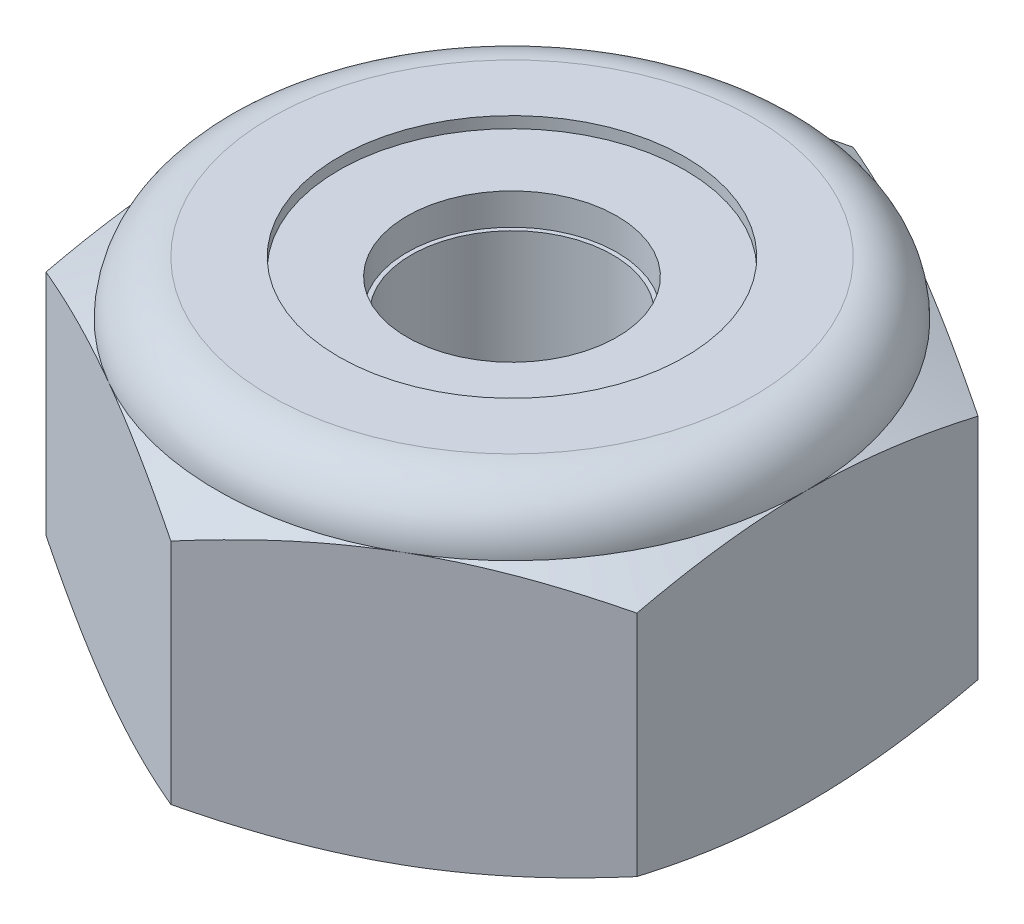
SolidWorks part; units mm, degrees
material "Alloy Steel"
ref_plane "Front" through (0, 0, 0) normal (0, 0, 1) x (1, 0, 0)
ref_plane "Top" through (0, 0, 0) normal (0, 1, 0) x (1, 0, 0)
ref_plane "Right" through (0, 0, 0) normal (1, 0, 0) x (0, 0, -1)
sketch "Sketch1" plane through (0, 0, 0) normal (0, 1, 0) x (1, 0, 0)
  line L1 (0, 4.5827) -> (-3.9688, 2.2914)
  line L2 (-3.9688, 2.2914) -> (-3.9688, -2.2914)
  line L3 (-3.9688, -2.2914) -> (0, -4.5827)
  line L4 (0, -4.5827) -> (3.9688, -2.2914)
  line L5 (3.9688, -2.2914) -> (3.9687, 2.2914)
  line L6 (3.9687, 2.2914) -> (0, 4.5827)
  circle A0 centre (0, 0) radius 3.9688 construction
  dimension "Hex Flats" = 7.9375
extrude "Extrude1" add sketch "Sketch1" along normal blind 4.3656
sketch "Sketch2" plane through (0, 0, 0) normal (1, 0, 0) x (0, 0, -1)
  line L0 (-1.7526, 0) -> (-1.7526, 4.3656) construction
  line L1 (0, 0) -> (1.7526, 0)
  line L2 (0, 0) -> (0, 4.3656)
  line L3 (0, 4.3656) -> (1.7526, 4.3656)
  line L4 (1.7526, 0) -> (1.7526, 4.3656)
  line L5 (-2.2914, 4.3656) -> (2.2914, 4.3656) construction
  line L7 (0, -1.7526) -> (0, 0) construction
  dimension "Thread Dia" = 3.5052
revolve "Revolve1" add sketch "Sketch2" angle 360 about L7
sketch "Sketch3" plane through (0, 0, 0) normal (1, 0, 0) x (0, 0, -1)
  line L0 (1.7526, 4.3656) -> (-1.7526, 4.3656) construction
  line L1 (-1.7526, 4.3656) -> (-1.7526, 3.5719) construction
  line L2 (-1.7526, 3.5719) -> (1.7526, 4.3656) construction
  line L3 (1.7526, 4.3656) -> (1.7745, 4.2689) construction
  line L4 (1.7745, 4.2689) -> (1.9279, 3.5915)
  line L5 (1.9279, 3.5915) -> (1.4541, 3.7385)
  line L6 (1.4541, 3.7385) -> (1.4103, 3.932)
  line L7 (1.4103, 3.932) -> (1.7745, 4.2689)
  line L8 (1.4322, 3.8353) -> (1.8512, 3.9302) construction
  line L9 (1.7526, 4.3656) -> (1.7526, 3.9078) construction
  line L10 (1.7526, 3.9078) -> (-1.7526, 3.1141) construction
  line L11 (-1.7526, 3.1141) -> (-1.7526, 3.5719) construction
  line L12 (-0.1935, 4.3656) -> (0.1935, 2.6563) construction
  line L13 (-1.7526, 0) -> (-1.7526, 4.3656) construction
  line L14 (0, 4.3656) -> (1.7526, 4.3656) construction
  line L15 (1.7526, 0) -> (1.7526, 4.3656) construction
  point P13 (0, 3.511)
  dimension "D1" = 0.0992
  dimension "D2" = 0.1984
  dimension "Thread Pitch" = 0.7937
  dimension "D4" = 60
  dimension "D5" = 0.7937
revolve "Cut-Revolve1" cut sketch "Sketch3" angle 360 about L12
pattern_linear "LPattern1" count 6 spacing 0.7937 along (0, -1, 0) count 2 spacing 0.7937 along (0, 1, 0) of "Cut-Revolve1"
sketch "Sketch4" plane through (0, 0, 0) normal (1, 0, 0) x (0, 0, -1)
  line L0 (0, 4.3656) -> (1.7526, 4.3656)
  line L1 (1.7526, 4.3656) -> (1.4103, 4.206)
  line L2 (1.4103, 4.206) -> (1.4103, 0.1596)
  line L3 (1.4103, 0.1596) -> (1.7526, 0)
  line L4 (1.7526, 0) -> (0, 0)
  line L5 (0, 0) -> (0, 4.3656)
  line L6 (1.7526, 0) -> (1.7526, 4.3656) construction
  line L7 (0, 4.3656) -> (1.7526, 4.3656) construction
  line L8 (0, 0) -> (1.7526, 0) construction
  line L9 (0, 0) -> (0, 4.3656) construction
  line L10 (0, 4.3656) -> (0, 4.7433) construction
  dimension "D1" = 25
revolve "Cut-Revolve2" cut sketch "Sketch4" angle 360 about L10
combine bodies "Combine1" operation type subtract main body 112 bodies to subtract 111
sketch "Sketch5" plane through (0, 0, 0) normal (1, 0, 0) x (0, 0, -1)
  line L0 (0, 0) -> (3.9688, 0)
  line L1 (3.9688, 0) -> (4.5827, 0.2863)
  line L2 (4.5827, 0.2863) -> (4.5827, 3.3517)
  line L3 (4.5827, 3.3517) -> (3.9687, 3.638)
  line L4 (3.2411, 4.3656) -> (3.2411, 5.6356)
  line L5 (3.2411, 5.6356) -> (5.8527, 5.6356)
  line L6 (5.8527, 5.6356) -> (5.8527, -1.27)
  line L7 (5.8527, -1.27) -> (0, -1.27)
  line L8 (0, -1.27) -> (0, 0)
  line L9 (3.9687, 3.638) -> (3.9688, 0) construction
  line L10 (0, 0) -> (1.7526, 0) construction
  line L13 (4.5827, 1.819) -> (5.8527, 1.819) construction
  line L14 (4.5827, 4.3656) -> (4.5827, 0) construction
  line L15 (0, 0) -> (0, 5.6356) construction
  line L20 (0, 5.6356) -> (3.2411, 5.6356) construction
  line L22 (0, 4.3656) -> (1.7526, 4.3656) construction
  arc A0 (3.9687, 3.638) -> (3.2411, 4.3656) centre (3.2411, 3.638) ccw
  dimension "D1" = 25
  dimension "D2" = 1.27
  dimension "D3" = 4.3656
  dimension "D4" = 0.7276
revolve "Cut-Revolve3" cut sketch "Sketch5" angle 360 about L15
sketch "Sketch6" plane through (0, 0, 0) normal (1, 0, 0) x (0, 0, -1)
  line L0 (0, 3.638) -> (3.8163, 3.638)
  line L1 (3.2411, 4.2132) -> (2.3257, 4.2132)
  line L2 (0, 5.6356) -> (0, 3.638)
  line L3 (2.3257, 5.6356) -> (0, 5.6356)
  line L4 (0, 5.6356) -> (3.2411, 5.6356) construction
  line L5 (0, 0) -> (0, 5.6356) construction
  line L6 (0, 5.6356) -> (0, 44.323) construction
  line L7 (2.3257, 4.2132) -> (2.3257, 5.6356)
  line L8 (3.2411, 4.3656) -> (3.2411, 4.2132) construction
  line L9 (2.3257, 4.2132) -> (1.4103, 4.2132) construction
  line L10 (1.4103, 4.2132) -> (1.4103, 4.206) construction
  arc A0 (3.8163, 3.638) -> (3.2411, 4.2132) centre (3.2411, 3.638) ccw
  arc A1 (3.9687, 3.638) -> (3.2411, 4.3656) centre (3.2411, 3.638) ccw construction
  dimension "D1" = 0.1524
revolve "Cut-Revolve4" cut sketch "Sketch6" angle 360 about L6
sketch "Sketch7" plane through (0, 0, 0) normal (1, 0, 0) x (0, 0, -1)
  line L0 (1.4103, 3.7142) -> (3.7343, 3.7142)
  line L1 (3.2411, 4.137) -> (1.4103, 4.137)
  line L2 (1.4103, 4.137) -> (1.4103, 3.7142)
  line L3 (1.4103, 3.7142) -> (0, 3.7142) construction
  line L4 (0, 3.7142) -> (0, 4.137) construction
  line L5 (0, 4.137) -> (1.4103, 4.137) construction
  line L6 (1.4103, 3.7142) -> (1.4103, 3.638) construction
  line L7 (0, 3.638) -> (3.8163, 3.638) construction
  line L8 (3.2411, 4.137) -> (3.2411, 4.2132) construction
  arc A0 (3.7343, 3.7142) -> (3.2411, 4.137) centre (3.2411, 3.638) ccw
  arc A2 (3.8163, 3.638) -> (3.2411, 4.2132) centre (3.2411, 3.638) ccw construction
  dimension "D1" = 0.0762
revolve "Revolve2" add sketch "Sketch7" angle 360 about L4
sketch "Sketch8" plane through (0, 0, 0) normal (0, -1, 0) x (1, 0, 0)
  circle A0 centre (0, 0) radius 2.1927
extrude "Boss-Extrude1" add sketch "Sketch8" against normal up to surface (3.7142 mm away) up to face at (0, 3.7142, -3.7343)
hole_wizard "#6-32 Tapped Hole1" positions "Sketch9" profile "Sketch10" tap size "#6-32" standard "ANSI Inch" end condition through all
sketch "Sketch9" plane through (0, 3.7142, 0) normal (0, 1, 0) x (1, 0, 0)
  point P0 (0, 0)
sketch "Sketch10" plane through (0, 3.7142, 0) normal (1, 0, 0) x (0, 0, 1)
  line L0 (0, 0) -> (0, 3.7142)
  line L1 (0, 3.7142) -> (1.9875, 3.7142)
  line L2 (1.3525, 3.0792) -> (1.3525, 0)
  line L5 (1.3525, 0) -> (0, 0)
  line L7 (1.9875, 3.7142) -> (1.3525, 3.0792)
  line L8 (-1.9876, 3.7142) -> (-1.3526, 3.0792) construction
  line L11 (0, -6.35) -> (0, 107.95) construction
  dimension "Thread Major Dia." = 2.7051
  dimension "Thru Tap Drill Depth" = 3.7142
  dimension "Far C'Sink Dia." = 3.9751
  dimension "Far C'Sink Angle" = 90
equation "\"D1@Sketch3\"=\"Thread Pitch@Sketch3\"/8"
equation "\"D2@Sketch3\"=\"Thread Pitch@Sketch3\"/4"
equation "\"D5@Sketch3\"=\"Thread Pitch@Sketch3\""
equation "\"D4@LPattern1\"=\"Thread Pitch@Sketch3\""
equation "\"D3@LPattern1\"=\"Thread Pitch@Sketch3\""
equation "\"D1@LPattern1\"=\"Height@Extrude1\"/\"Thread Pitch@Sketch3\""
equation "\"D4@Sketch5\"=\"Height@Extrude1\"/6"
